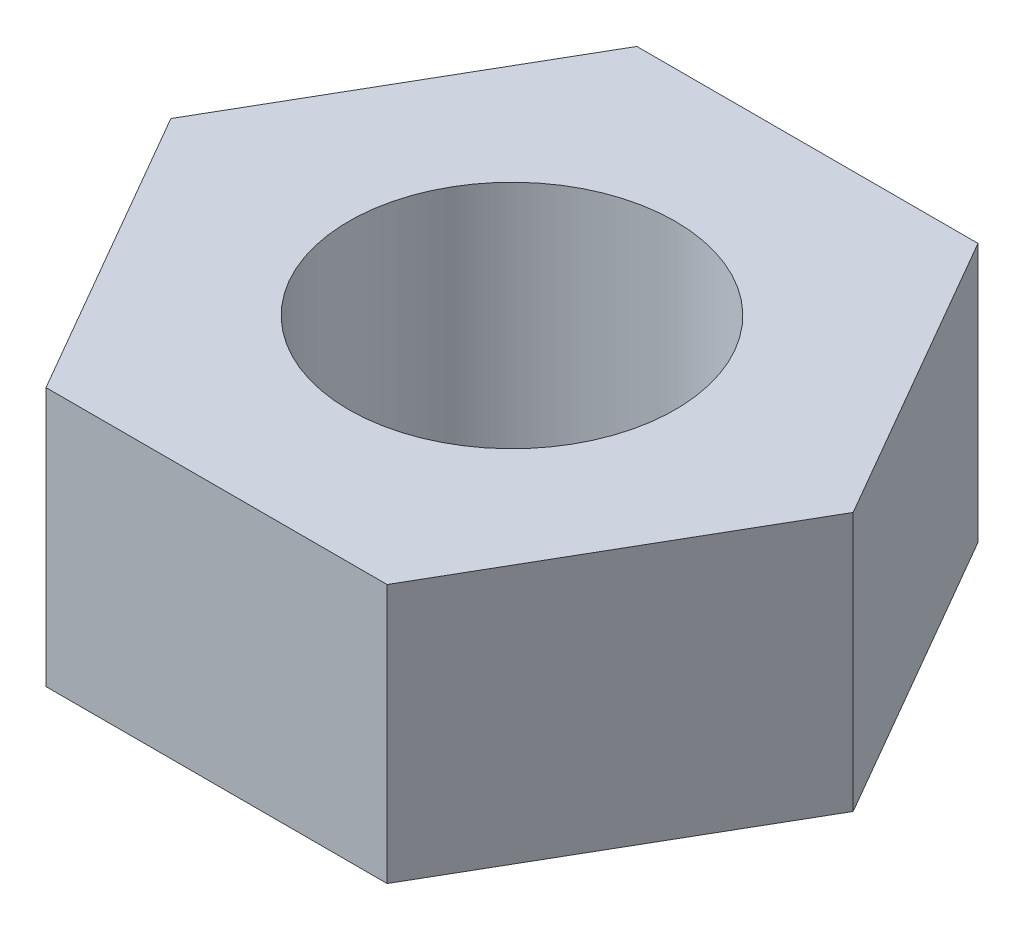
SolidWorks part; units mm, degrees
ref_plane "Front Plane" through (0, 0, 0) normal (0, 0, 1) x (1, 0, 0)
ref_plane "Top Plane" through (0, 0, 0) normal (0, 1, 0) x (1, 0, 0)
ref_plane "Right Plane" through (0, 0, 0) normal (1, 0, 0) x (0, 0, -1)
sketch "Sketch1" plane through (0, 0, 0) normal (0, 1, 0) x (1, 0, 0)
  line L1 (3.135, 0) -> (1.5675, 2.715)
  line L2 (1.5675, 2.715) -> (-1.5675, 2.715)
  line L3 (-1.5675, 2.715) -> (-3.135, 0)
  line L4 (-3.135, 0) -> (-1.5675, -2.715)
  line L5 (-1.5675, -2.715) -> (1.5675, -2.715)
  line L6 (1.5675, -2.715) -> (3.135, 0)
  circle A0 centre (0, 0) radius 1.5
  circle A1 centre (0, 0) radius 2.715 construction
  dimension "D2" = 3
  dimension "D1" = 5.43
extrude "Boss-Extrude1" add sketch "Sketch1" along normal blind 2.38
